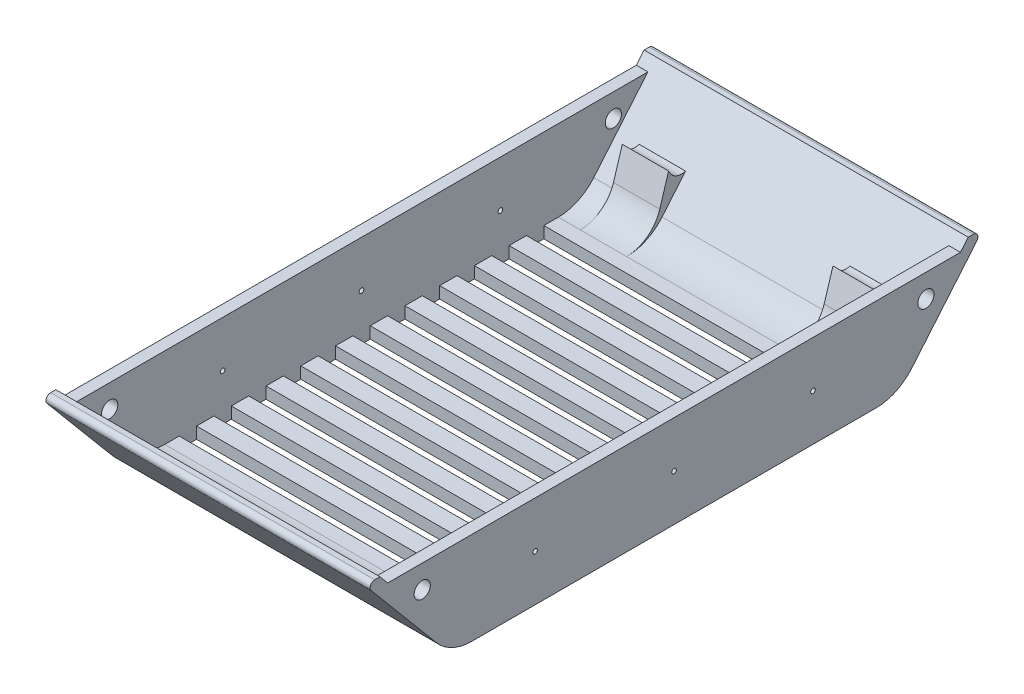
SolidWorks part; units mm, degrees
material "PLA"
ref_plane "Front Plane" through (0, 0, 0) normal (0, 0, 1) x (1, 0, 0)
ref_plane "Top Plane" through (0, 0, 0) normal (0, 1, 0) x (1, 0, 0)
ref_plane "Right Plane" through (0, 0, 0) normal (1, 0, 0) x (0, 0, -1)
sketch "Sketch4" plane through (0, 0, 0) normal (1, 0, 0) x (0, 0, -1)
  line L0 (0, 0) -> (87.3315, 0)
  line L1 (102.6524, 7.1442) -> (130.8212, 40.7144)
  line L2 (129.2891, 44) -> (127.051, 44)
  line L3 (127.051, 44) -> (100.3209, 12.1442)
  line L4 (85, 5) -> (0, 5)
  line L5 (0, 5) -> (0, 0)
  line L6 (0, 0) -> (0, 44) construction
  line L7 (127.051, 44) -> (130.8813, 40.7861) construction
  arc A0 (100.3209, 12.1442) -> (85, 5) centre (85, 25) cw
  arc A1 (87.3315, 0) -> (102.6524, 7.1442) centre (87.3315, 20) ccw
  arc A2 (130.8212, 40.7144) -> (129.2891, 44) centre (129.2891, 42) ccw
  point P14 (133.5781, 44)
  dimension "D5" = 20
  dimension "D2" = 2
  dimension "D1" = 5
  dimension "D3" = 39
  dimension "D4" = 50
  dimension "D6" = 170
  dimension "D7" = 267.1562
extrude "Boss-Extrude4" add sketch "Sketch4" along normal mid plane 140 contours L4 L5 L0 A1 L1 A2 L2 L3 A0
sketch "Esquisse15" plane through (0, 0, 0) normal (1, 0, 0) x (0, 0, -1)
  line L0 (100.3209, 12.1442) -> (110.4749, 24.2454)
  line L1 (85, 5) -> (0, 5) construction
  line L3 (127.051, 44) -> (100.3209, 12.1442) construction
  line L4 (99.337, 15.5898) -> (103.1385, 27.9479)
  line L5 (0, 0) -> (87.3315, 0) construction
  arc A1 (99.337, 15.5898) -> (85, 5) centre (85, 20) cw
  arc A2 (100.3209, 12.1442) -> (85, 5) centre (85, 25) cw
  arc A3 (85, 5) -> (100.3209, 12.1442) centre (85, 25) ccw construction
  arc A4 (110.4749, 24.2454) -> (103.1385, 27.9479) centre (108.7766, 30) cw
  arc A5 (85, 5) -> (100.3209, 12.1442) centre (85, 25) ccw construction
  dimension "D1" = 6
  dimension "D2" = 5
  dimension "D3" = 15
  dimension "D4" = 8
  dimension "D5" = 30
extrude "Boss.-Extru.5" add sketch "Esquisse15" against normal offset from surface 14.5 and the other way offset from surface (55.5 mm away) 14.5 up to face at (-70, 17.2327, -85.0107) other way up to face at (70, 17.2327, -85.0107)
sketch "Esquisse18" plane through (0, 0, 0) normal (1, 0, 0) x (0, 0, -1)
  line L0 (100.3209, 12.1442) -> (110.4749, 24.2454)
  line L4 (99.337, 15.5898) -> (103.1385, 27.9479)
  arc A1 (99.337, 15.5898) -> (85, 5) centre (85, 20) cw
  arc A2 (100.3209, 12.1442) -> (85, 5) centre (85, 25) cw
  arc A4 (110.4749, 24.2454) -> (103.1385, 27.9479) centre (108.7766, 30) cw
  arc A6 (85, 5) -> (100.3209, 12.1442) centre (85, 25) ccw construction
  dimension "D1" = 6
  dimension "D2" = 5
  dimension "D3" = 15
  dimension "D4" = 8
extrude "Enlèv. mat.-Extru.3" cut sketch "Esquisse18" against normal offset from surface 20 and the other way offset from surface (35.5 mm away) 20 up to face at (-55.5, 15.8831, -100.0147) other way up to face at (55.5, 15.8831, -100.0147)
mirror "Mirror2" about plane through (70, 5, 0) normal (0, 0, -1) of "Boss-Extrude4"
ref_plane "Plan1" through (0, 40, 0) normal (0, 1, 0) x (1, 0, 0)
sketch "Esquisse9" plane through (0, 40, 0) normal (0, 1, 0) x (1, 0, 0)
  line L0 (-65, -123.6946) -> (-70, 123.6946) construction
  line L1 (70, 123.6946) -> (65, 123.6946)
  line L2 (70, 123.6946) -> (70, -123.6946)
  line L3 (70, -123.6946) -> (65, -123.6946)
  line L4 (65, 123.6946) -> (65, -123.6946)
  line L5 (-70, -123.6946) -> (-65, 123.6946) construction
  line L6 (-70, 123.6946) -> (-65, 123.6946)
  line L7 (-70, 123.6946) -> (-70, -123.6946)
  line L8 (-70, -123.6946) -> (-65, -123.6946)
  line L9 (-65, 123.6946) -> (-65, -123.6946)
  dimension "D1" = 5
extrude "Boss.-Extru.3" add sketch "Esquisse9" against normal up to body separate body
sketch "Esquisse8" plane through (0, 0, 0) normal (1, 0, 0) x (0, 0, -1)
  line L0 (-87.3315, 0) -> (87.3315, 0) construction
  line L2 (0, 0) -> (0, 50) construction
  circle A3 centre (0, 30) radius 1 construction
  circle A4 centre (0, 20) radius 1
  circle A5 centre (60, 20) radius 1
  circle A9 centre (-60, 20) radius 1
  dimension "D1" = 60
  dimension "D2" = 20
extrude "Enlèv. mat.-Extru.1" cut sketch "Esquisse8" against normal through all both and the other way through all
sketch "Esquisse17" plane through (0, 5, 0) normal (0, 1, 0) x (1, 0, 0)
  line L0 (-70, 85) -> (-70, -85) construction
  line L1 (65, 3.75) -> (-65, 3.75)
  line L2 (65, 3.75) -> (65, -3.75)
  line L3 (65, -3.75) -> (-65, -3.75)
  line L4 (-65, 3.75) -> (-65, -3.75)
  line L5 (65, 3.75) -> (-65, -3.75) construction
  line L6 (65, -3.75) -> (-65, 3.75) construction
  line L7 (65, 18.75) -> (65, 11.25)
  line L8 (65, 18.75) -> (-65, 18.75)
  line L9 (-65, 18.75) -> (-65, 11.25)
  line L10 (65, 11.25) -> (-65, 11.25)
  line L11 (65, 33.75) -> (65, 26.25)
  line L12 (65, 33.75) -> (-65, 33.75)
  line L13 (-65, 33.75) -> (-65, 26.25)
  line L14 (65, 26.25) -> (-65, 26.25)
  line L15 (65, 48.75) -> (65, 41.25)
  line L16 (65, 48.75) -> (-65, 48.75)
  line L17 (-65, 48.75) -> (-65, 41.25)
  line L18 (65, 41.25) -> (-65, 41.25)
  line L19 (65, 63.75) -> (65, 56.25)
  line L20 (65, 63.75) -> (-65, 63.75)
  line L21 (-65, 63.75) -> (-65, 56.25)
  line L22 (65, 56.25) -> (-65, 56.25)
  line L23 (65, 78.75) -> (65, 71.25)
  line L24 (65, 78.75) -> (-65, 78.75)
  line L25 (-65, 78.75) -> (-65, 71.25)
  line L26 (65, 71.25) -> (-65, 71.25)
  line L27 (65, -11.25) -> (65, -18.75)
  line L28 (65, -11.25) -> (-65, -11.25)
  line L29 (-65, -11.25) -> (-65, -18.75)
  line L30 (65, -18.75) -> (-65, -18.75)
  line L31 (65, -26.25) -> (65, -33.75)
  line L32 (65, -26.25) -> (-65, -26.25)
  line L33 (-65, -26.25) -> (-65, -33.75)
  line L34 (65, -33.75) -> (-65, -33.75)
  line L35 (65, -41.25) -> (65, -48.75)
  line L36 (65, -41.25) -> (-65, -41.25)
  line L37 (-65, -41.25) -> (-65, -48.75)
  line L38 (65, -48.75) -> (-65, -48.75)
  line L39 (65, -56.25) -> (65, -63.75)
  line L40 (65, -56.25) -> (-65, -56.25)
  line L41 (-65, -56.25) -> (-65, -63.75)
  line L42 (65, -63.75) -> (-65, -63.75)
  line L43 (65, -71.25) -> (65, -78.75)
  line L44 (65, -71.25) -> (-65, -71.25)
  line L45 (-65, -71.25) -> (-65, -78.75)
  line L46 (65, -78.75) -> (-65, -78.75)
  point P0 (0, 0)
  dimension "D1" = 7.5
  dimension "D3" = 15
  dimension "D5" = 15
  dimension "D6" = 5
  dimension "D2" = 6
  dimension "D4" = 6
extrude "Enlèv. mat.-Extru.2" cut sketch "Esquisse17" against normal through all both and the other way through all
sketch "Esquisse19" plane through (-65, 0, 0) normal (1, 0, 0) x (0, 0, -1)
  line L0 (100.3209, 12.1442) -> (112.6078, 26.7872) construction
  line L1 (100.3209, 12.1442) -> (123.6946, 40) construction
  line L3 (112.6078, 26.7872) -> (106.6895, 31.7532) construction
  circle A0 centre (108.7776, 30.0011) radius 3.5
  dimension "D1" = 19.115
  dimension "D2" = 7
  dimension "D3" = 5
extrude "Enlèv. mat.-Extru.4" cut sketch "Esquisse19" against normal through all both and the other way through all
mirror "Symétrie1" about plane through (0, 0, 0) normal (0, 0, 1) of "Enlèv. mat.-Extru.4"
